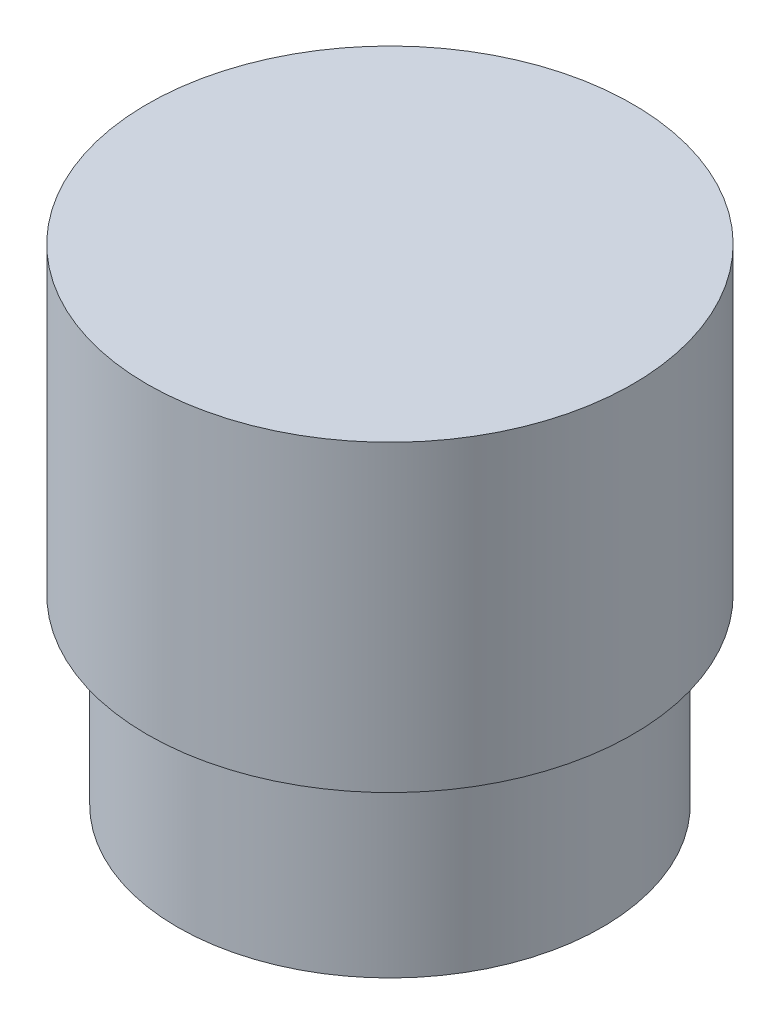
SolidWorks part; units mm, degrees
ref_plane "Front Plane" through (0, 0, 0) normal (0, 0, 1) x (1, 0, 0)
ref_plane "Top Plane" through (0, 0, 0) normal (0, 1, 0) x (1, 0, 0)
ref_plane "Right Plane" through (0, 0, 0) normal (1, 0, 0) x (0, 0, -1)
sketch "Sketch1" plane through (0, 0, 0) normal (0, 0, 1) x (1, 0, 0)
  line L0 (0, 0) -> (3.5, 0)
  line L1 (3.5, 0) -> (3.5, 3)
  line L2 (3.5, 3) -> (4, 3)
  line L3 (4, 3) -> (4, 8)
  line L4 (4, 8) -> (0, 8)
  line L5 (0, 8) -> (0, 0)
  dimension "D1" = 8
  dimension "D2" = 3.5
  dimension "D3" = 4
  dimension "D4" = 3
revolve "Revolve1" add sketch "Sketch1" angle 360 about L5
sketch "Sketch2" plane through (0, 0, 0) normal (0, -1, 0) x (1, 0, 0)
  circle A0 centre (0, 0) radius 2.775
  dimension "D1" = 5.55
extrude "Cut-Extrude1" cut sketch "Sketch2" against normal blind 3
